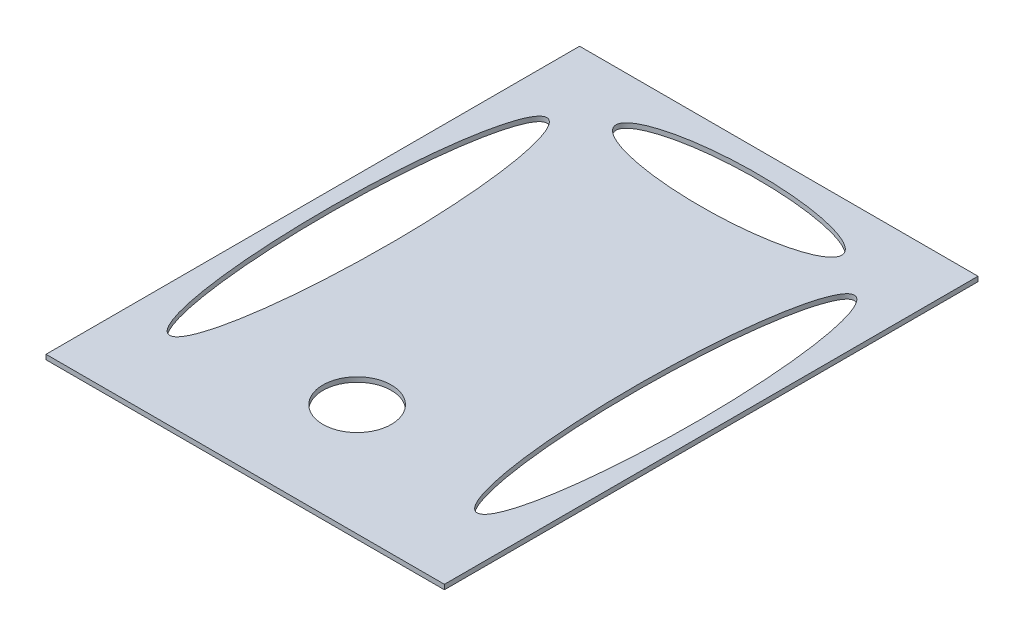
SolidWorks part; units mm, degrees
material "Thornel Mat VMA"
ref_plane "前视基准面" through (0, 0, 0) normal (0, 0, 1) x (1, 0, 0)
ref_plane "上视基准面" through (0, 0, 0) normal (0, 1, 0) x (1, 0, 0)
ref_plane "右视基准面" through (0, 0, 0) normal (1, 0, 0) x (0, 0, -1)
sketch "草图1" plane through (0, 0, 0) normal (0, 1, 0) x (1, 0, 0)
  line L1 (-47.5799, 504.6245) -> (369.4201, 504.6245)
  line L2 (-47.5799, 504.6245) -> (-47.5799, -53.8755)
  line L3 (-47.5799, -53.8755) -> (369.4201, -53.8755)
  line L4 (369.4201, 504.6245) -> (369.4201, -53.8755)
extrude "凸台-拉伸1" add sketch "草图1" along normal blind 5
sketch "草图2" plane through (0, 5, 0) normal (0, 1, 0) x (1, 0, 0)
  line L0 (160.9201, 504.6245) -> (160.9201, -53.8755) construction
  line L1 (369.4201, 504.6245) -> (-47.5799, 504.6245) construction
  line L2 (-47.5799, -53.8755) -> (369.4201, -53.8755) construction
  line L3 (-47.5799, 225.3745) -> (365.2302, 225.3745) construction
  line L4 (-47.5799, 504.6245) -> (-47.5799, -53.8755) construction
  line L5 (160.9201, -53.8755) -> (160.9201, 63.2505) construction
  circle A0 centre (160.9201, 63.2505) radius 35.8
  ellipse E0 centre (0, 225.3745) end of major axis (0, 422.7876) minor radius 32.2358
  ellipse E1 centre (160.9201, 452.4282) end of major axis (42.7445, 452.4282) minor radius 29.6406
  ellipse E2 centre (321.8402, 225.3745) end of major axis (321.8402, 422.7876) minor radius 32.2358
  dimension "D1" = 117.126
extrude "切除-拉伸1" cut sketch "草图2" against normal through all contours E0 | E2 | A0 | E1
